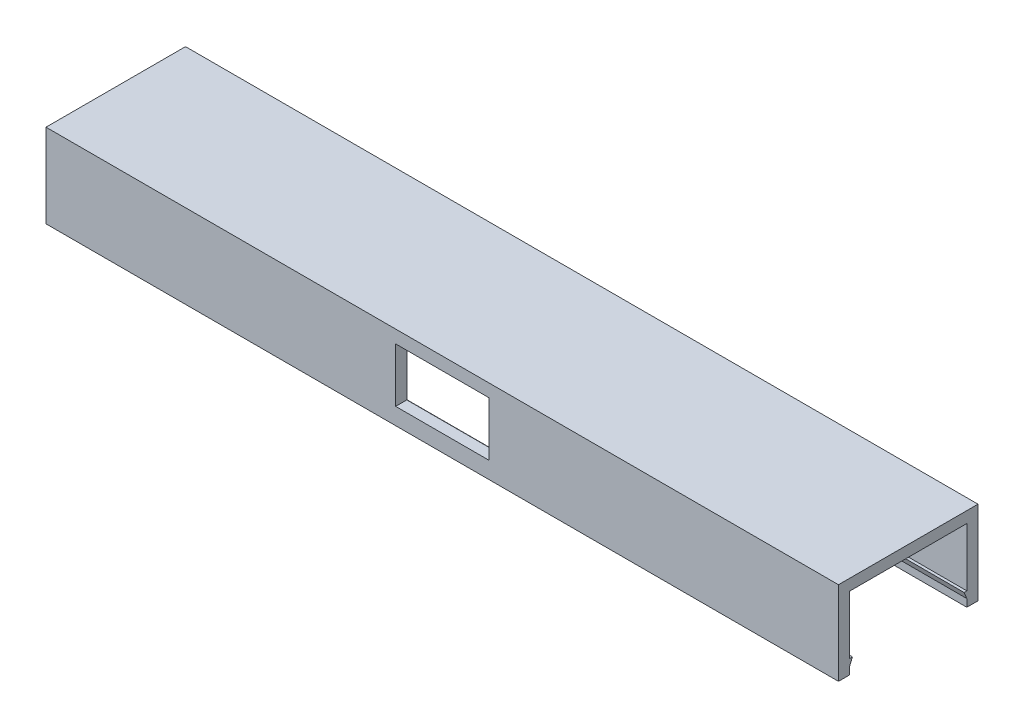
SolidWorks part; units mm, degrees
ref_plane "Front Plane" through (0, 0, 0) normal (0, 0, 1) x (1, 0, 0)
ref_plane "Top Plane" through (0, 0, 0) normal (0, 1, 0) x (1, 0, 0)
ref_plane "Right Plane" through (0, 0, 0) normal (1, 0, 0) x (0, 0, -1)
sketch "Croquis1" plane through (0, 0, 0) normal (0, 1, 0) x (1, 0, 0)
  line L0 (-71, -12.5) -> (-71, 12.5)
  line L1 (-71, -12.5) -> (71, -12.5)
  line L2 (-71, 12.5) -> (71, 12.5)
  line L3 (71, -12.5) -> (71, 12.5)
  line L4 (-71, -12.5) -> (71, 12.5) construction
  line L5 (-71, 12.5) -> (71, -12.5) construction
  line L6 (71, -10.35) -> (71, 10.35)
  line L7 (71, -10.35) -> (-71, -10.35)
  line L8 (71, 10.35) -> (-71, 10.35)
  line L9 (-71, -10.35) -> (-71, 10.35)
  line L10 (71, -10.35) -> (-71, 10.35) construction
  line L11 (71, 10.35) -> (-71, -10.35) construction
  point P1 (0, 0)
  point P2 (0, 0)
  dimension "D1" = 142
  dimension "D2" = 25
  dimension "D3" = 142
  dimension "D4" = 2.15
extrude "Saliente-Extruir1" add sketch "Croquis1" along normal blind 15 contours L3 L8 L0 L7 | L8 L3 L2 L0 | L3 L7 L0 L1
sketch "Croquis2" plane through (-71, 0, 0) normal (-1, 0, 0) x (0, 0, 1)
  line L0 (-10.5, 13) -> (-10.5, 0)
  line L1 (-10.5, 13) -> (10.5, 13)
  line L2 (-10.5, 0) -> (10.5, 0)
  line L3 (10.5, 13) -> (10.5, 0)
  line L4 (-10.5, 13) -> (10.5, 0) construction
  line L5 (-10.5, 0) -> (10.5, 13) construction
  line L6 (-12.5, 15) -> (-12.5, 0) construction
  line L11 (12.5, 15) -> (-12.5, 15) construction
  line L13 (12.5, 0) -> (-12.5, 0) construction
  line L14 (12.5, 15) -> (12.5, 0) construction
  point P1 (0, 6.5)
  dimension "D1" = 2
  dimension "D2" = 2
  dimension "D3" = 2
  dimension "D4" = 6.5
extrude "Cortar-Extruir1" cut sketch "Croquis2" against normal blind 230
sketch "Croquis11" plane through (-71, 0, 0) normal (-1, 0, 0) x (0, 0, 1)
  line L0 (-10.5, 1.35) -> (-10.5, 2.55)
  line L1 (-10.5, 0) -> (-12.5, 0) construction
  line L2 (-10.5, 13) -> (-10.5, 0) construction
  line L3 (-10.5, 2.55) -> (-10, 2.55)
  line L4 (-10, 2.55) -> (-10.5, 1.35)
  line L6 (0, 0) -> (0, 8.3198) construction
  line L11 (10.5, 13) -> (-10.5, 13) construction
  line L13 (10, 2.55) -> (10.5, 1.35)
  line L14 (10.5, 2.55) -> (10, 2.55)
  line L15 (10.5, 1.35) -> (10.5, 2.55)
  dimension "D1" = 10.45
  dimension "D2" = 1.35
  dimension "D3" = 0.5
extrude "Saliente-Extruir4" add sketch "Croquis11" against normal up to surface (142 mm away) up to face at (71, 7, 0)
sketch "Croquis12" plane through (0, 0, 12.5) normal (0, 0, 1) x (1, 0, 0)
  line L0 (-8.35, 3) -> (8.35, 3)
  line L1 (-8.35, 3) -> (-8.35, 12.7)
  line L2 (8.35, 3) -> (8.35, 12.7)
  line L3 (-8.35, 12.7) -> (8.35, 12.7)
  line L4 (-8.35, 3) -> (8.35, 12.7) construction
  line L5 (8.35, 3) -> (-8.35, 12.7) construction
  line L6 (-71, 0) -> (71, 0) construction
  point P1 (0, 7.85)
  point P3 (0, 0)
  point P8 (0, 0)
  dimension "D1" = 16.7
  dimension "D2" = 9.7
  dimension "D3" = 3
extrude "Cortar-Extruir2" cut sketch "Croquis12" against normal blind 50
